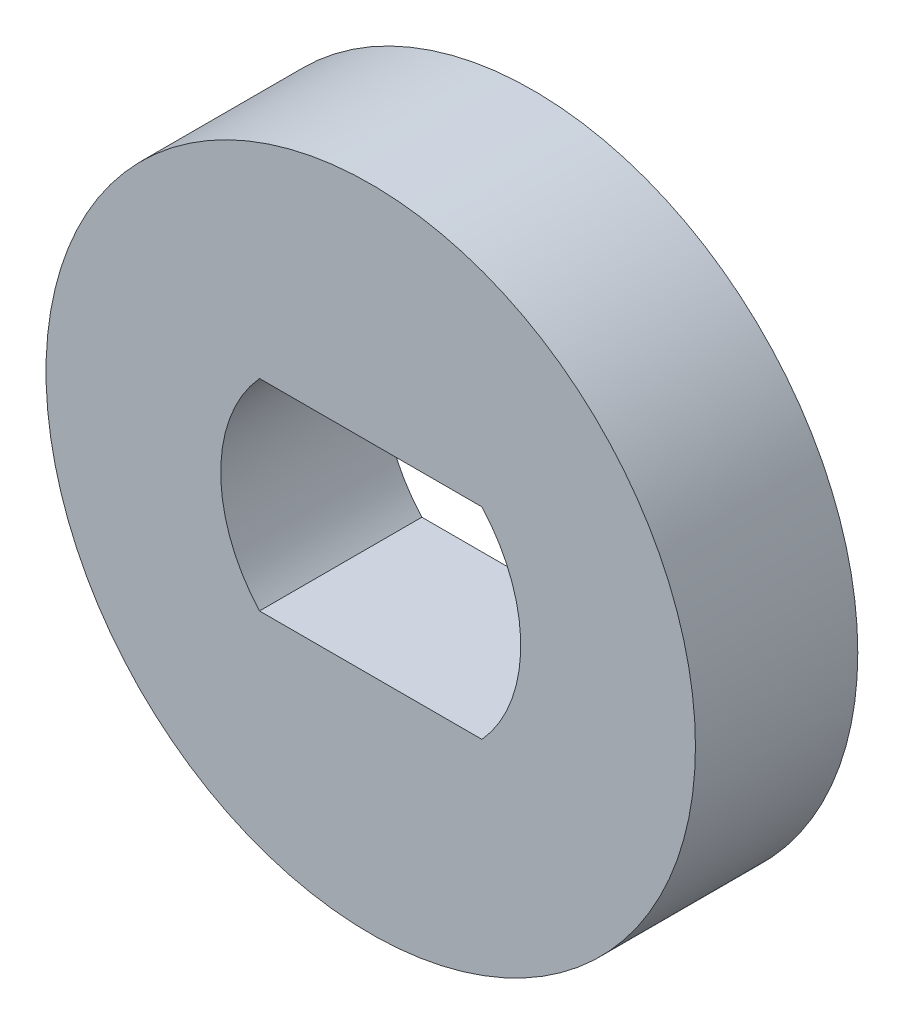
SolidWorks part; units mm, degrees
ref_plane "Front Plane" through (0, 0, 0) normal (0, 0, 1) x (1, 0, 0)
ref_plane "Top Plane" through (0, 0, 0) normal (0, 1, 0) x (1, 0, 0)
ref_plane "Right Plane" through (0, 0, 0) normal (1, 0, 0) x (0, 0, -1)
sketch "Sketch1" plane through (0, 0, 0) normal (0, 0, 1) x (1, 0, 0)
  line L1 (-2.1752, 1.9685) -> (2.1752, 1.9685)
  line L2 (-2.1752, 1.9685) -> (-2.1752, -1.9685)
  line L3 (-2.1752, -1.9685) -> (2.1752, -1.9685)
  line L4 (2.1752, 1.9685) -> (2.1752, -1.9685)
  circle A0 centre (0, 0) radius 6.35
  arc A1 (2.1752, -1.9685) -> (2.1752, 1.9685) centre (0, 0) ccw
  arc A2 (-2.1752, 1.9685) -> (-2.1752, -1.9685) centre (0, 0) ccw
  dimension "D1" = 12.7
  dimension "D2" = 2.9337
  dimension "D3" = 3.937
extrude "Boss-Extrude1" add sketch "Sketch1" along normal blind 3.175 contours A0 A2 L1 A1 L3
